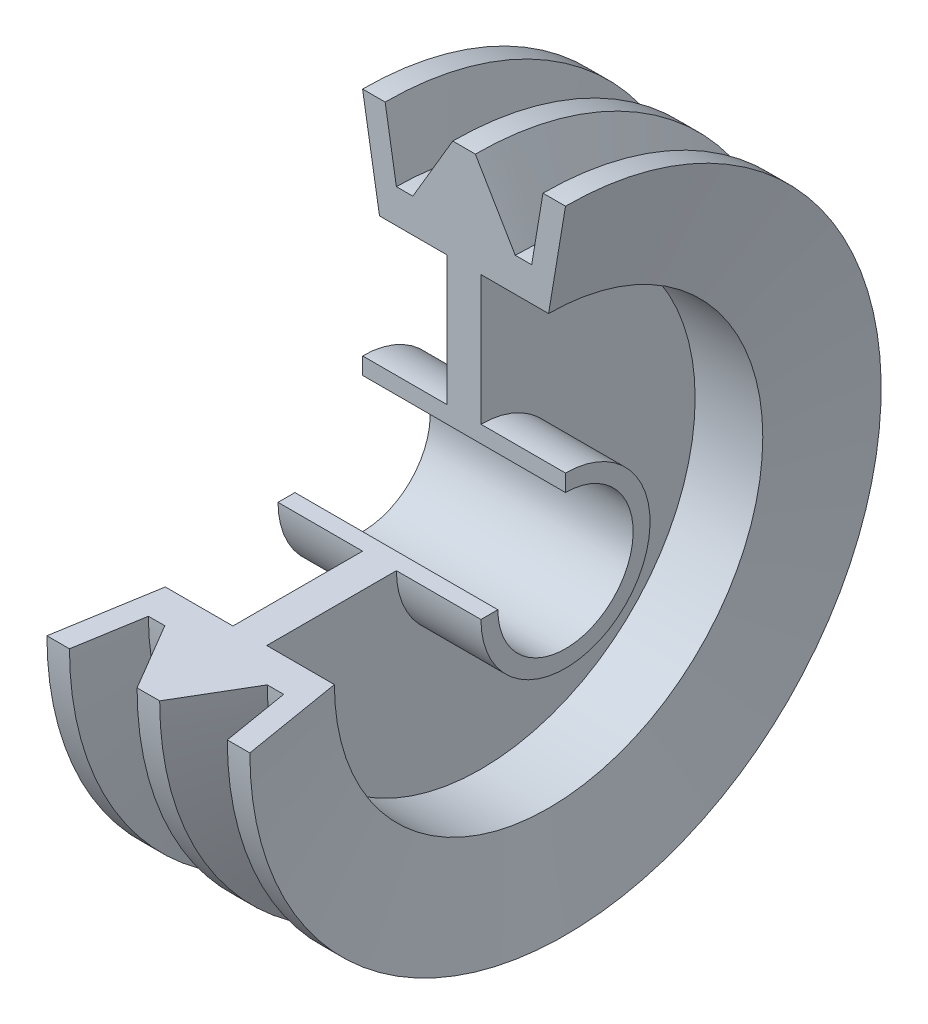
SolidWorks part; units mm, degrees
ref_plane "Front Plane" through (0, 0, 0) normal (0, 0, 1) x (1, 0, 0)
ref_plane "Top Plane" through (0, 0, 0) normal (0, 1, 0) x (1, 0, 0)
ref_plane "Right Plane" through (0, 0, 0) normal (1, 0, 0) x (0, 0, -1)
sketch "Sketch1" plane through (0, 0, 0) normal (0, 0, 1) x (1, 0, 0)
  line L0 (-35.4425, -19.2104) -> (54.5575, -19.2104)
  line L1 (54.5575, -19.2104) -> (54.5575, -11.7104)
  line L2 (-35.4425, -19.2104) -> (-35.4425, -11.7104)
  line L3 (54.5575, 90.7896) -> (44.5575, 90.7896)
  line L4 (-35.4425, -11.7104) -> (2.0575, -11.7104) construction
  line L5 (-35.4425, -11.7104) -> (2.0575, -11.7104)
  line L6 (54.5575, -11.7104) -> (17.0575, -11.7104)
  line L7 (17.0575, -11.7104) -> (17.0575, 45.7896)
  line L8 (2.0575, -11.7104) -> (2.0575, 45.7896)
  line L9 (9.5575, -19.2104) -> (9.5575, -49.2104) construction
  line L10 (17.0575, -11.7104) -> (54.5575, -11.7104) construction
  line L12 (4.5575, 90.8062) -> (14.5713, 90.7896)
  line L14 (-35.4425, 90.7896) -> (-25.4425, 90.7896)
  line L15 (17.0575, 45.7896) -> (47.0575, 45.7896)
  line L16 (54.5575, 90.7896) -> (47.0575, 45.7896)
  line L19 (14.5575, 90.8062) -> (14.5713, 90.7896)
  line L20 (14.5575, 90.8062) -> (32.2652, 60.7896)
  line L22 (14.5713, 90.7896) -> (14.5575, 90.7896) construction
  line L24 (2.0575, 45.7896) -> (-27.9425, 45.7896)
  line L25 (44.5575, 90.7896) -> (39.5575, 60.7896)
  line L26 (32.2652, 60.7896) -> (39.5575, 60.7896) construction
  line L27 (32.2652, 60.7896) -> (39.5575, 60.7896)
  line L29 (-25.4425, 90.7896) -> (-20.4425, 60.7896)
  line L30 (-20.4425, 60.7896) -> (-13.1503, 60.7896)
  line L31 (-27.9425, 45.7896) -> (-35.4425, 90.7896)
  line L32 (-20.4425, 60.7896) -> (-13.1503, 60.7896) construction
  line L33 (4.5575, 90.8062) -> (-13.1503, 60.7896)
  line L36 (-35.4425, -49.2104) -> (54.5575, -49.2104) construction
  point P19 (9.5575, 90.8062)
revolve "Revolve5" add sketch "Sketch1" angle 270 about L36
